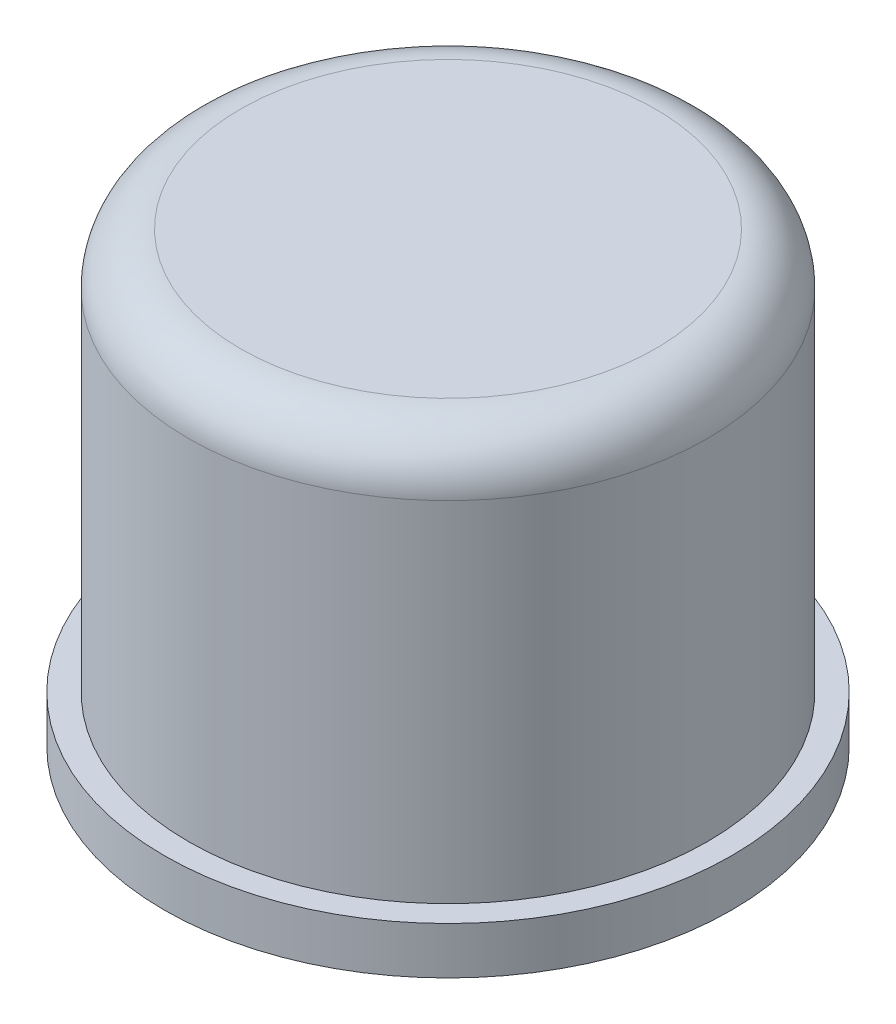
SolidWorks part; units mm, degrees
ref_plane "Front Plane" through (0, 0, 0) normal (0, 0, 1) x (1, 0, 0)
ref_plane "Top Plane" through (0, 0, 0) normal (0, 1, 0) x (1, 0, 0)
ref_plane "Right Plane" through (0, 0, 0) normal (1, 0, 0) x (0, 0, -1)
sketch "Sketch2" plane through (0, 0, 0) normal (0, 1, 0) x (1, 0, 0)
  circle A0 centre (0, 0) radius 1100
extrude "Boss-Extrude1" add sketch "Sketch2" along normal blind 1700
fillet "Fillet1" radius 220 1 edges at (0, 1700, 1100)
sketch "Sketch3" plane through (0, 0, 0) normal (0, -1, 0) x (1, 0, 0)
  circle A0 centre (0, 0) radius 1202.8898
extrude "Boss-Extrude2" add sketch "Sketch3" along normal blind 200
